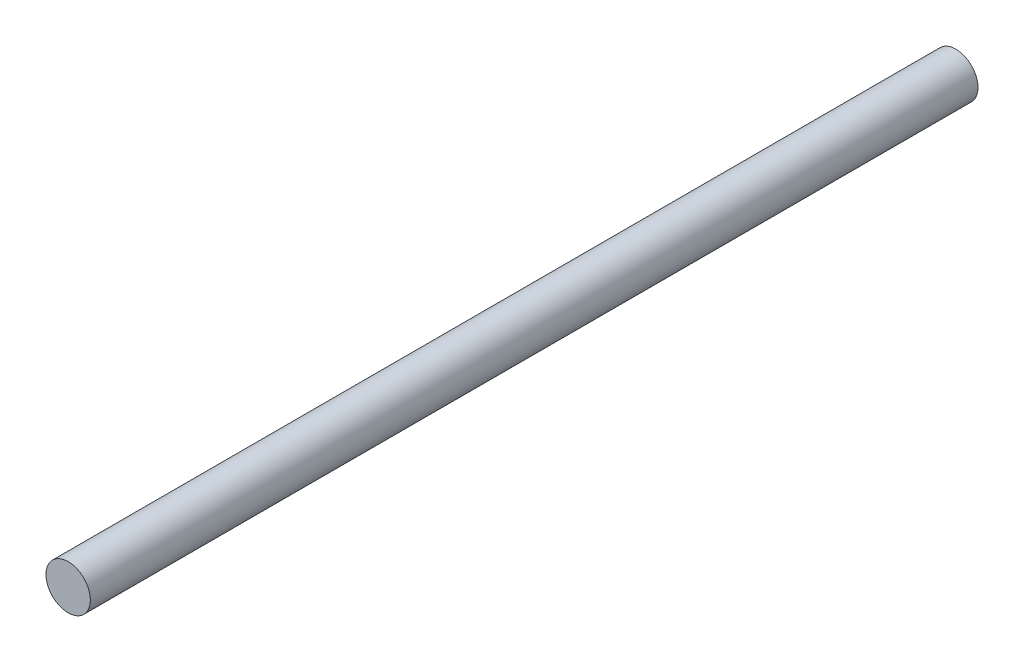
SolidWorks part; units mm, degrees
ref_plane "Front Plane" through (0, 0, 0) normal (0, 0, 1) x (1, 0, 0)
ref_plane "Top Plane" through (0, 0, 0) normal (0, 1, 0) x (1, 0, 0)
ref_plane "Right Plane" through (0, 0, 0) normal (1, 0, 0) x (0, 0, -1)
sketch "Sketch1" plane through (0, 0, 0) normal (0, 0, 1) x (1, 0, 0)
  circle A0 centre (0, 0) radius 4
  dimension "D1" = 8
extrude "Boss-Extrude1" add sketch "Sketch1" along normal blind 160
